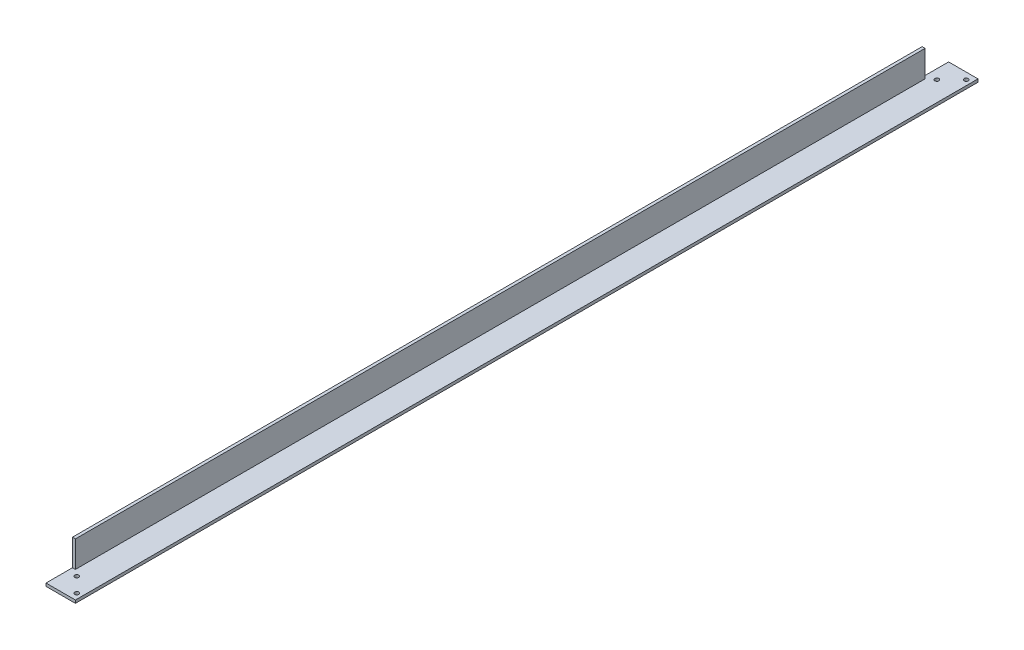
SolidWorks part; units mm, degrees
ref_plane "Plan de face" through (0, 0, 0) normal (0, 0, 1) x (1, 0, 0)
ref_plane "Plan de dessus" through (0, 0, 0) normal (0, 1, 0) x (1, 0, 0)
ref_plane "Plan de droite" through (0, 0, 0) normal (1, 0, 0) x (0, 0, -1)
sketch "Esquisse1" plane through (0, 0, 0) normal (0, 0, 1) x (1, 0, 0)
  line L0 (0, 0) -> (20, 0)
  line L1 (20, 0) -> (20, 2)
  line L2 (20, 2) -> (2, 2)
  line L3 (2, 2) -> (2, 20)
  line L4 (2, 20) -> (0, 20)
  line L5 (0, 20) -> (0, 0)
  dimension "D1" = 20
  dimension "D2" = 2
extrude "Boss.-Extru.1" add sketch "Esquisse1" along normal blind 614
sketch "Esquisse2" plane through (2, 0, 0) normal (1, 0, 0) x (0, 0, -1)
  line L0 (-614, 2) -> (0, 2) construction
  line L1 (-614, 20) -> (-596, 20)
  line L2 (-614, 20) -> (-614, 2)
  line L3 (-614, 2) -> (-596, 2)
  line L4 (-596, 20) -> (-596, 2)
  line L5 (-614, 2) -> (0, 2) construction
  line L6 (0, 20) -> (-18, 20)
  line L7 (0, 20) -> (0, 2)
  line L8 (0, 2) -> (-18, 2)
  line L9 (-18, 20) -> (-18, 2)
  dimension "D1" = 18
extrude "Enlèv. mat.-Extru.1" cut sketch "Esquisse2" against normal through all
sketch "Esquisse6" plane through (0, 2, 0) normal (0, 1, 0) x (1, 0, 0)
  line L0 (20, -307) -> (2, -307) construction
  line L1 (20, -614) -> (20, 0) construction
  line L2 (2, -596) -> (2, -18) construction
  line L3 (20, -614) -> (0, -614) construction
  line L4 (2, -596) -> (2, -18) construction
  line L5 (0, -614) -> (0, -596) construction
  circle A0 centre (6.48, -599.52) radius 1.4
  circle A1 centre (6.48, -14.48) radius 1.4
  circle A2 centre (16.48, -609.52) radius 1.4
  circle A3 centre (16.48, -4.48) radius 1.4
  dimension "D3" = 2.8
  dimension "D1" = 14.48
  dimension "D2" = 4.48
  dimension "D4" = 4.48
  dimension "D5" = 16.48
extrude "Enlèv. mat.-Extru.5" cut sketch "Esquisse6" against normal through all
